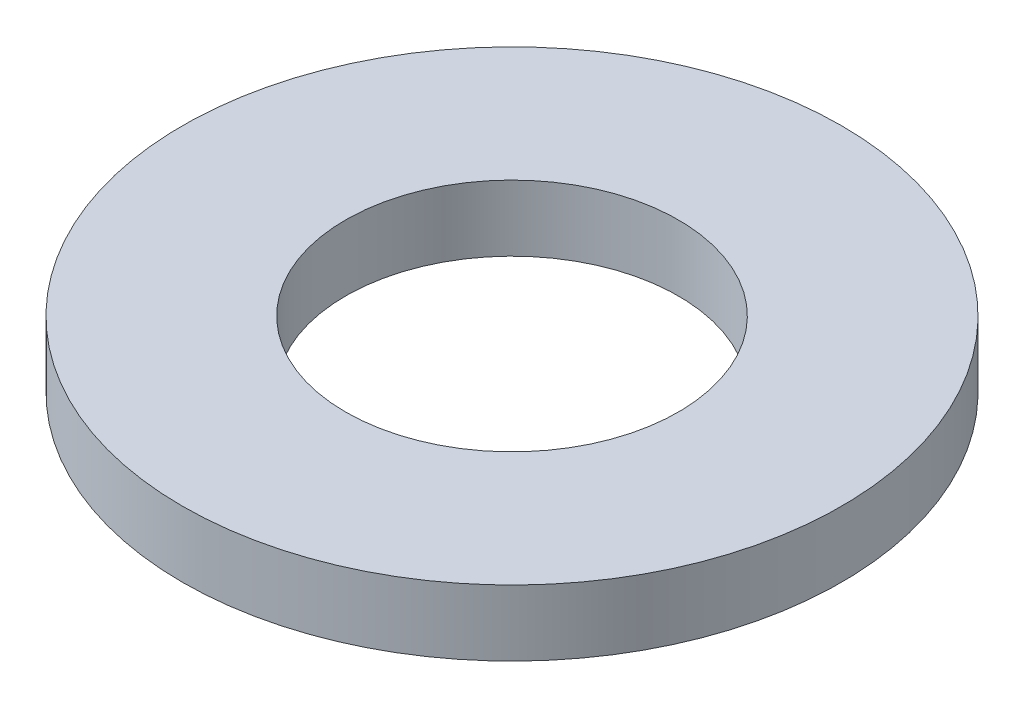
SolidWorks part; units mm, degrees
ref_plane "Front Plane" through (0, 0, 0) normal (0, 0, 1) x (1, 0, 0)
ref_plane "Top Plane" through (0, 0, 0) normal (0, 1, 0) x (1, 0, 0)
ref_plane "Right Plane" through (0, 0, 0) normal (1, 0, 0) x (0, 0, -1)
sketch "Sketch1" plane through (0, 0, 0) normal (0, 1, 0) x (1, 0, 0)
  circle A0 centre (0, 0) radius 5
  circle A1 centre (0, 0) radius 2.525
  dimension "D1" = 5.05
  dimension "D2" = 10
extrude "Boss-Extrude1" add sketch "Sketch1" along normal blind 1
